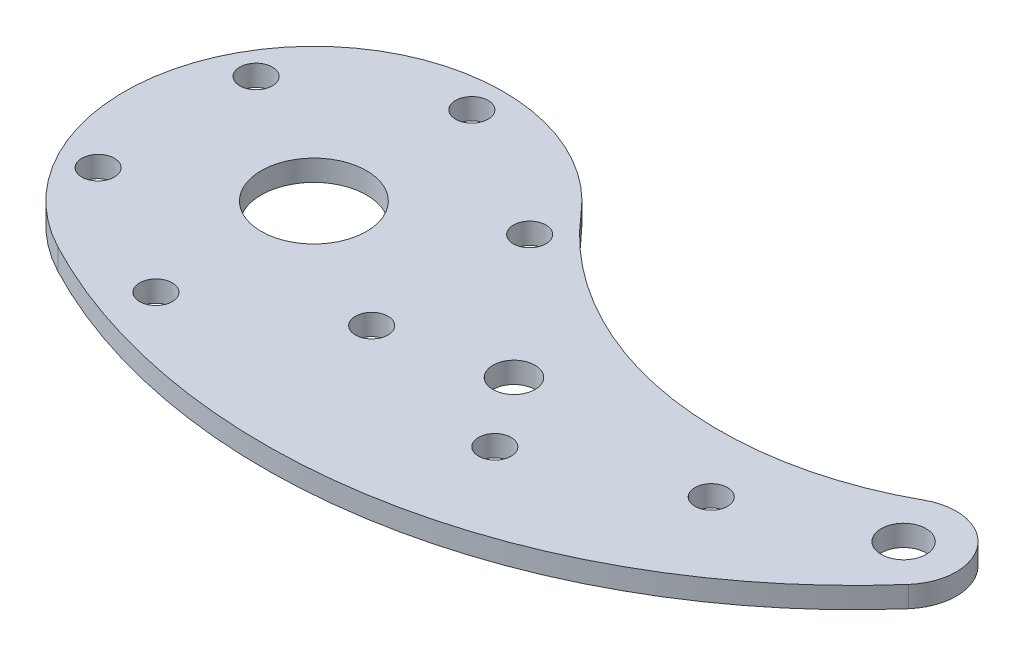
SolidWorks part; units mm, degrees
material "6061-T6 (SS)"
ref_plane "Front" through (0, 0, 0) normal (0, 0, 1) x (1, 0, 0)
ref_plane "Top" through (0, 0, 0) normal (0, 1, 0) x (1, 0, 0)
ref_plane "Right" through (0, 0, 0) normal (1, 0, 0) x (0, 0, -1)
sketch "Sketch1" plane through (0, 0, 0) normal (0, 1, 0) x (1, 0, 0)
  arc A0 (21.7731, 18.5057) -> (-13.2871, -25.2979) centre (0, 0) ccw
  circle A1 centre (0, 0) radius 7.9375
  arc A2 (94.8656, -5.2359) -> (85.0596, 6.9466) centre (88.9, 0) ccw
  circle A3 centre (88.9, 0) radius 3.3782
  arc A5 (21.7731, 18.5057) -> (85.0596, 6.9466) centre (60.4809, 51.4048) ccw
  arc A6 (-13.2871, -25.2979) -> (94.8656, -5.2359) centre (28.0506, 53.4067) ccw
  dimension "D2" = 57.15
  dimension "D3" = 15.875
  dimension "D4" = 6.7564
  dimension "D1" = 15.875
  dimension "D6" = 50.8
  dimension "D7" = 88.9
  dimension "D5" = 88.9
extrude "Boss-Extrude1" add sketch "Sketch1" along normal blind 3.175
sketch "Sketch4" plane through (0, 3.175, 0) normal (0, 1, 0) x (1, 0, 0)
  circle A0 centre (0, 0) radius 23.8125
  point P7 (-20.6222, 11.9062)
  point P9 (20.6222, 11.9062)
  point P11 (20.6222, -11.9062)
  point P13 (-20.6222, -11.9062)
  point P14 (0, 23.8125)
  point P16 (0, -23.8125)
  dimension "D1" = 47.625
  dimension "D2" = 23.8125
hole_wizard "#10 (0.1935) Diameter Hole1" positions "Sketch4" profile "Sketch3" hole size "#10" standard "ANSI Inch" end condition through all
sketch "Sketch3" plane through (0, 3.175, 23.8125) normal (1, 0, 0) x (0, 0, 1)
  line L0 (0, 0) -> (0, 3.175)
  line L1 (0, 3.175) -> (2.4574, 3.175)
  line L2 (2.4574, 3.175) -> (2.4574, 0)
  line L5 (2.4574, 0) -> (0, 0)
  line L11 (0, -6.35) -> (0, 107.95) construction
  dimension "Thru Hole Dia." = 4.9149
  dimension "Thru Hole Depth" = 3.175
sketch "Sketch7" plane through (0, 3.175, 0) normal (0, 1, 0) x (1, 0, 0)
  line L3 (38.1, -7.9375) -> (88.9, 0) construction
  line L6 (0, 0) -> (88.9, 0) construction
  circle A0 centre (88.9, 0) radius 3.3782 construction
  point P0 (38.1, -7.9375)
  dimension "D1" = 7.9375
  dimension "D2" = 50.8
hole_wizard "1/4 (0.25) Diameter Hole2" positions "Sketch7" profile "Sketch8" hole size "1/4" standard "ANSI Inch" end condition through all
sketch "Sketch8" plane through (38.1, 3.175, 7.9375) normal (1, 0, 0) x (0, 0, 1)
  line L0 (0, 0) -> (0, 3.175)
  line L1 (0, 3.175) -> (3.175, 3.175)
  line L2 (3.175, 3.175) -> (3.175, 0)
  line L5 (3.175, 0) -> (0, 0)
  line L11 (0, -6.35) -> (0, 107.95) construction
  dimension "Thru Hole Dia." = 6.35
  dimension "Thru Hole Depth" = 3.175
sketch "Sketch11" plane through (0, 3.175, 0) normal (0, 1, 0) x (1, 0, 0)
  line L4 (45.72, -18.4452) -> (88.9, 0) construction
  arc A0 (94.8656, -5.2359) -> (85.0596, 6.9466) centre (88.9, 0) ccw construction
  circle A1 centre (88.9, 0) radius 3.3782 construction
  arc A4 (21.7731, 18.5057) -> (85.0596, 6.9466) centre (60.4809, 51.4048) ccw construction
  point P0 (68.58, -8.6801)
  point P2 (45.72, -18.4452)
  point P51 (45.72, -33.7197)
  point P55 (45.72, -14.2495)
  point P56 (45.72, -15.6367)
  point P57 (45.72, -17.8362)
  dimension "D1" = 43.18
  dimension "D2" = 20.32
  dimension "D3" = 69.85
hole_wizard "#10 (0.1935) Diameter Hole2" positions "Sketch11" profile "Sketch10" hole size "#10" standard "ANSI Inch"
sketch "Sketch10" plane through (68.58, 3.175, 8.6801) normal (1, 0, 0) x (0, 0, 1)
  line L0 (0, 0) -> (0, 13.5162)
  line L1 (0, 13.5162) -> (2.4574, 12.0396)
  line L2 (2.4574, 12.0396) -> (2.4574, 0)
  line L5 (2.4574, 0) -> (0, 0)
  line L10 (0, 13.5162) -> (-2.4575, 12.0396) construction
  line L11 (0, -6.35) -> (0, 107.95) construction
  dimension "Hole Dia." = 4.9149
  dimension "Hole Depth" = 12.0396
  dimension "Drill Angle" = 118
